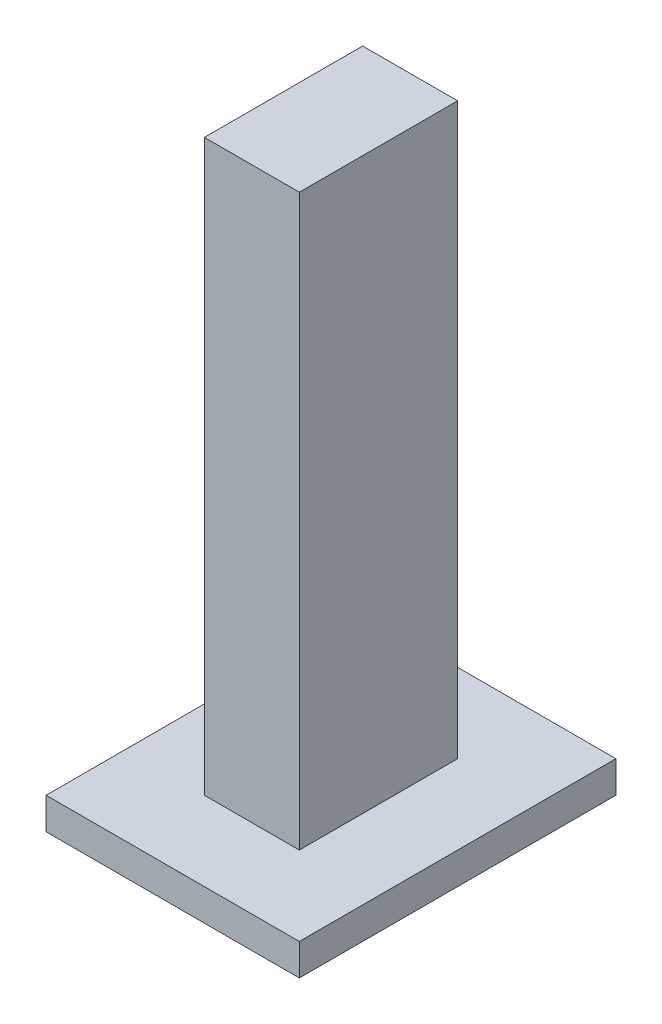
SolidWorks part; units mm, degrees
ref_plane "Ebene vorne" through (0, 0, 0) normal (0, 0, 1) x (1, 0, 0)
ref_plane "Ebene oben" through (0, 0, 0) normal (0, 1, 0) x (1, 0, 0)
ref_plane "Ebene rechts" through (0, 0, 0) normal (1, 0, 0) x (0, 0, -1)
sketch "Skizze1" plane through (0, 0, 0) normal (0, 0, 1) x (1, 0, 0)
  line L1 (-15, 45) -> (0, 45)
  line L2 (-15, 45) -> (-15, -45)
  line L3 (-15, -45) -> (0, -45)
  line L4 (0, 45) -> (0, -45)
  dimension "D1" = 90
  dimension "D2" = 15
extrude "Aufsatz-Linear austragen1" add sketch "Skizze1" along normal blind 25
sketch "Skizze2" plane through (0, -45, 0) normal (0, -1, 0) x (1, 0, 0)
  line L1 (-7.5, 36.9082) -> (-7.5, -19.0085) construction
  line L2 (-27.5, 37.5) -> (12.5, 37.5)
  line L3 (-27.5, 37.5) -> (-27.5, -12.5)
  line L4 (-27.5, -12.5) -> (12.5, -12.5)
  line L5 (12.5, 37.5) -> (12.5, -12.5)
  line L6 (-15, 25) -> (-15, 0) construction
  line L7 (0, 25) -> (0, 0) construction
  line L8 (-29.5, 12.5) -> (18.57, 12.5) construction
  line L9 (-15, 25) -> (0, 25) construction
  line L10 (-15, 0) -> (0, 0) construction
  dimension "D1" = 50
  dimension "D2" = 40
extrude "Aufsatz-Linear austragen2" add sketch "Skizze2" along normal blind 5
